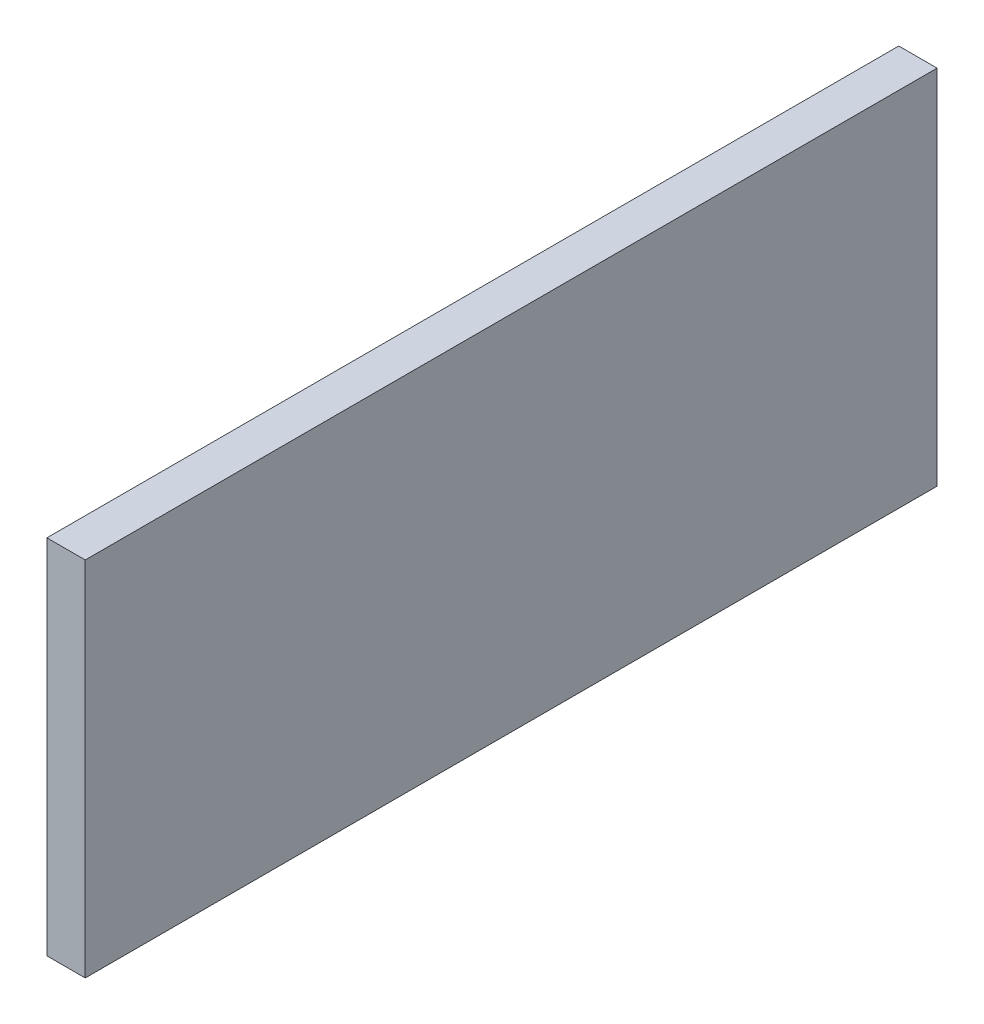
SolidWorks part; units mm, degrees
ref_plane "Спереди" through (0, 0, 0) normal (0, 0, 1) x (1, 0, 0)
ref_plane "Сверху" through (0, 0, 0) normal (0, 1, 0) x (1, 0, 0)
ref_plane "Справа" through (0, 0, 0) normal (1, 0, 0) x (0, 0, -1)
sketch "Эскиз1" plane through (0, 0, 0) normal (1, 0, 0) x (0, 0, -1)
  line L1 (-39.7682, 18.7522) -> (360.2318, 18.7522)
  line L2 (-39.7682, 18.7522) -> (-39.7682, -151.2478)
  line L3 (-39.7682, -151.2478) -> (360.2318, -151.2478)
  line L4 (360.2318, 18.7522) -> (360.2318, -151.2478)
  dimension "D1" = 400
  dimension "D2" = 170
extrude "Бобышка-Вытянуть1" add sketch "Эскиз1" along normal blind 18
